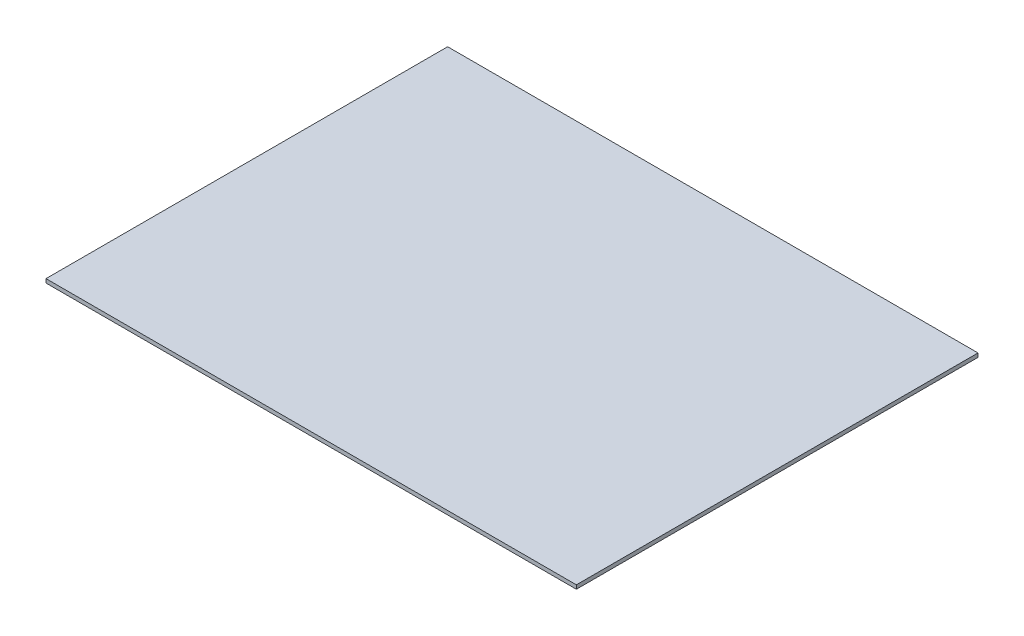
SolidWorks part; units mm, degrees
ref_plane "Front Plane" through (0, 0, 0) normal (0, 0, 1) x (1, 0, 0)
ref_plane "Top Plane" through (0, 0, 0) normal (0, 1, 0) x (1, 0, 0)
ref_plane "Right Plane" through (0, 0, 0) normal (1, 0, 0) x (0, 0, -1)
sketch "Sketch1" plane through (0, 0, 0) normal (0, 1, 0) x (1, 0, 0)
  line L0 (186.0677, 350.475) -> (186.0677, 38.475) construction
  line L5 (-225.9323, 38.475) -> (186.0677, 38.475) construction
  line L6 (-225.9323, 350.475) -> (186.0677, 350.475) construction
  line L7 (-225.9323, 350.475) -> (-225.9323, 38.475) construction
  line L8 (186.0677, 350.475) -> (186.0677, 38.475)
  line L9 (-225.9323, 38.475) -> (186.0677, 38.475)
  line L10 (-225.9323, 350.475) -> (186.0677, 350.475)
  line L11 (-225.9323, 350.475) -> (-225.9323, 38.475)
extrude "Boss-Extrude1" add sketch "Sketch1" along normal blind 3
